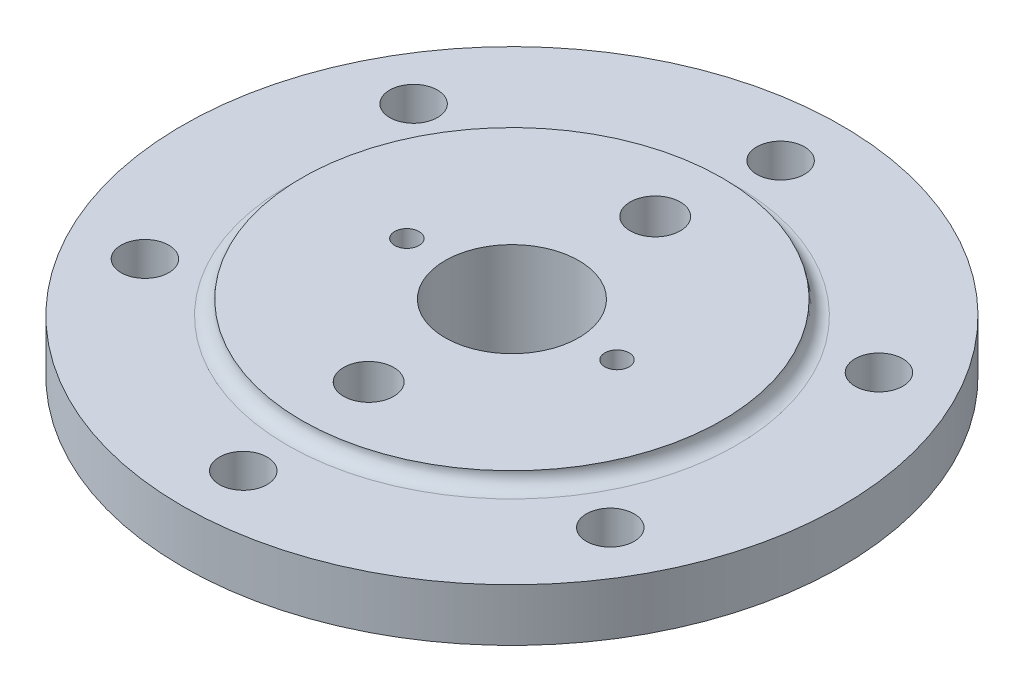
SolidWorks part; units mm, degrees
ref_plane "Front Plane" through (0, 0, 0) normal (0, 0, 1) x (1, 0, 0)
ref_plane "Top Plane" through (0, 0, 0) normal (0, 1, 0) x (1, 0, 0)
ref_plane "Right Plane" through (0, 0, 0) normal (1, 0, 0) x (0, 0, -1)
sketch "Sketch1" plane through (0, 0, 0) normal (1, 0, 0) x (0, 0, -1)
  line L0 (0, 40.8228) -> (0, -43.4878) construction
  line L1 (14, 0) -> (35, 0)
  line L2 (35, 0) -> (81, 47)
  line L3 (81, 47) -> (81, 53)
  line L4 (81, 53) -> (138, 53)
  line L5 (138, 53) -> (138, 75)
  line L6 (138, 75) -> (94, 75)
  line L7 (88, 81) -> (28, 81)
  line L8 (28, 81) -> (28, 33)
  line L9 (51.2338, 0) -> (-71.0958, 0) construction
  line L10 (28, 33) -> (14, 24.9171)
  line L11 (14, 24.9171) -> (14, 0)
  arc A2 (88, 81) -> (94, 75) centre (94, 81) ccw
  dimension "D13" = 6
  dimension "D14" = 6
  dimension "D1" = 14
  dimension "D2" = 28
  dimension "D3" = 88
  dimension "D4" = 138
  dimension "D5" = 81
  dimension "D6" = 35
  dimension "D7" = 47
  dimension "D8" = 6
  dimension "D9" = 22
  dimension "D10" = 6
  dimension "D11" = 48
  dimension "D12" = 60
revolve "Revolve1" add sketch "Sketch1" angle 360 about L0
sketch "Sketch2" plane through (0, 75, 0) normal (0, 1, 0) x (1, 0, 0)
  line L0 (0, 0) -> (0, 112.5) construction
  circle A0 centre (0, 112.5) radius 10
  circle A1 centre (97.4279, 56.25) radius 10
  circle A2 centre (97.4279, -56.25) radius 10
  circle A3 centre (0, -112.5) radius 10
  circle A4 centre (-97.4279, -56.25) radius 10
  circle A5 centre (-97.4279, 56.25) radius 10
  point P16 (0, 0)
  dimension "D2" = 20
  dimension "D1" = 112.5
  dimension "D3" = 6
extrude "Cut-Extrude1" cut sketch "Sketch2" against normal through all
hole_wizard "M24 Tapped Hole3" positions "Sketch6" profile "Sketch7" tap size "M24" standard "ISO"
sketch "Sketch6" plane through (0, 81, 0) normal (0, 1, 0) x (1, 0, 0)
  line L0 (0, 60) -> (0, -60) construction
  point P1 (0, 60)
  point P2 (0, -60)
  point P8 (0, 0)
  point P18 (-5.7872, -5.0321)
  point P20 (0, -60)
  point P22 (0, 60)
  dimension "D1" = 120
sketch "Sketch7" plane through (0, 81, -60) normal (1, 0, 0) x (0, 0, 1)
  line L0 (0, 0) -> (0, 33.309)
  line L1 (0, 33.309) -> (10.5, 27)
  line L2 (10.5, 27) -> (10.5, 0)
  line L5 (10.5, 0) -> (0, 0)
  line L10 (0, 33.309) -> (-10.5, 27) construction
  line L11 (0, -6.35) -> (0, 107.95) construction
  dimension "Tap Drill Dia." = 21
  dimension "Tap Drill Depth" = 27
  dimension "Drill Angle" = 118
cosmetic thread "Hole Thread1" parameters "D1"=24, "D2"=24
cosmetic thread "Hole Thread2" parameters "D1"=24, "D2"=24
sketch "Sketch11" plane through (0, 81, 0) normal (0, 1, 0) x (1, 0, 0)
  line L0 (-44, 0) -> (44, 0) construction
  point P3 (0, 0)
  dimension "D1" = 88
hole_wizard "M12 Tapped Hole1" positions "Sketch12" profile "Sketch13" tap size "M12" standard "ISO"
sketch "Sketch12" plane through (0, 81, 0) normal (0, 1, 0) x (1, 0, 0)
  point P0 (-44, 0)
  point P3 (44, 0)
sketch "Sketch13" plane through (-44, 81, 0) normal (1, 0, 0) x (0, 0, 1)
  line L0 (0, 0) -> (0, 18.0644)
  line L1 (0, 18.0644) -> (5.1, 15)
  line L2 (5.1, 15) -> (5.1, 0)
  line L5 (5.1, 0) -> (0, 0)
  line L10 (0, 18.0644) -> (-5.1, 15) construction
  line L11 (0, -6.35) -> (0, 107.95) construction
  dimension "Tap Drill Dia." = 10.2
  dimension "Tap Drill Depth" = 15
  dimension "Drill Angle" = 118
cosmetic thread "Hole Thread3" parameters "D1"=12, "D2"=12
cosmetic thread "Hole Thread4" parameters "D1"=12, "D2"=12
